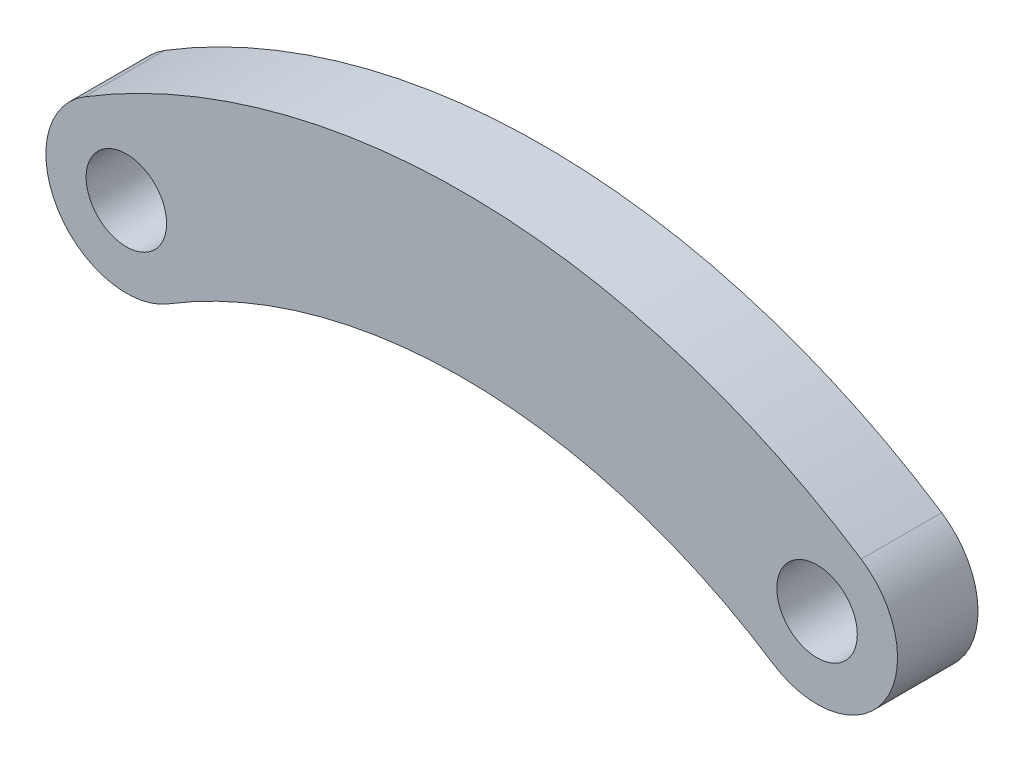
SolidWorks part; units mm, degrees
ref_plane "Front Plane" through (0, 0, 0) normal (0, 0, 1) x (1, 0, 0)
ref_plane "Top Plane" through (0, 0, 0) normal (0, 1, 0) x (1, 0, 0)
ref_plane "Right Plane" through (0, 0, 0) normal (1, 0, 0) x (0, 0, -1)
sketch "Sketch1" plane through (0, 0, 0) normal (0, 0, 1) x (1, 0, 0)
  arc A0 (-10.723, 0.9788) -> (15.0214, 0.5841) centre (1.8381, -19.5063) cw construction
  arc A1 (16.6673, 3.0923) -> (-12.2912, 3.5363) centre (1.8381, -19.5063) ccw
  arc A2 (13.3755, -1.9241) -> (-9.1548, -1.5787) centre (1.8381, -19.5063) ccw
  arc A3 (13.3755, -1.9241) -> (16.6673, 3.0923) centre (15.0214, 0.5841) ccw
  arc A4 (-12.2912, 3.5363) -> (-9.1548, -1.5787) centre (-10.723, 0.9788) ccw
  circle A5 centre (-10.723, 0.9788) radius 1.5
  circle A6 centre (15.0214, 0.5841) radius 1.5
  point P3 (2.2065, 4.5205)
  dimension "D2" = 6
  dimension "D3" = 3
  dimension "D1" = 25.7474
extrude "Boss-Extrude1" add sketch "Sketch1" along normal blind 3 contours A1 A4 A2 A3
